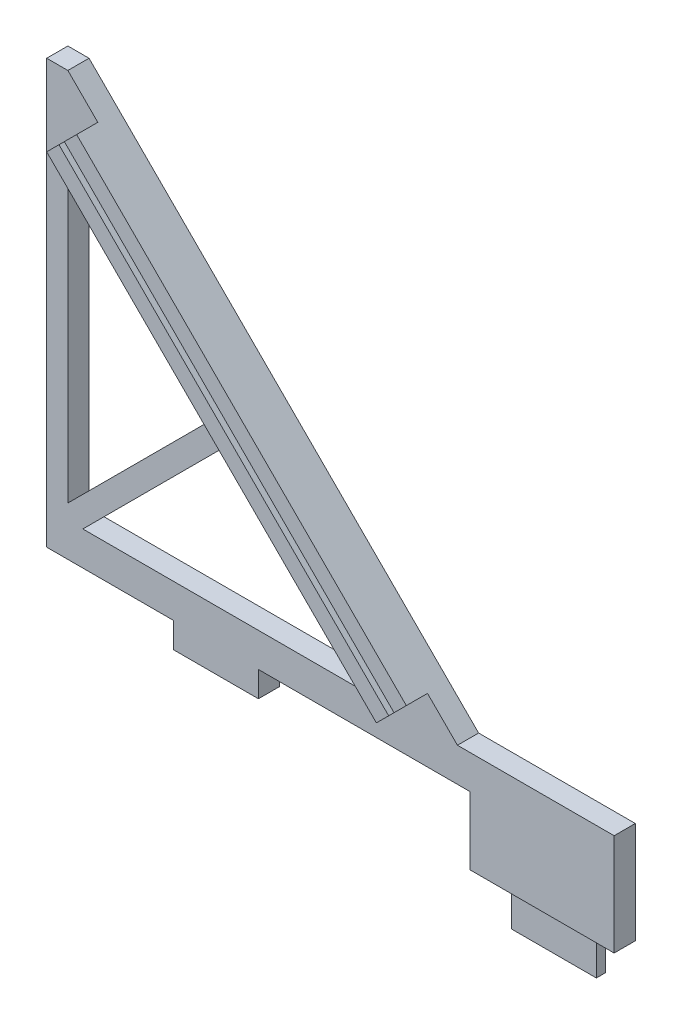
SolidWorks part; units mm, degrees
ref_plane "Front Plane" through (0, 0, 0) normal (0, 0, 1) x (1, 0, 0)
ref_plane "Top Plane" through (0, 0, 0) normal (0, 1, 0) x (1, 0, 0)
ref_plane "Right Plane" through (0, 0, 0) normal (1, 0, 0) x (0, 0, -1)
sketch "Sketch2" plane through (0, 0, 0) normal (0, 0, 1) x (1, 0, 0)
  line L0 (0, 0) -> (12.7, 0)
  line L1 (12.7, 0) -> (12.7, 6.35)
  line L2 (12.7, 6.35) -> (17.145, 6.35)
  line L3 (17.145, 6.35) -> (17.145, 21.59)
  line L5 (0, 0) -> (0, 6.35)
  line L6 (0, 6.35) -> (-4.445, 6.35)
  line L7 (-4.445, 6.35) -> (-4.445, 16.51)
  line L11 (-64.77, 80.01) -> (-67.945, 80.01)
  line L13 (-48.895, 16.51) -> (-48.895, 12.7)
  line L14 (-67.945, 80.01) -> (-67.945, 16.51)
  line L15 (-67.945, 16.51) -> (-48.895, 16.51)
  line L18 (-48.895, 12.7) -> (-36.195, 12.7)
  line L19 (-36.195, 12.7) -> (-36.195, 16.51)
  line L20 (-36.195, 16.51) -> (-4.445, 16.51)
  line L21 (17.145, 21.59) -> (-6.35, 21.59)
  line L22 (-6.35, 21.59) -> (-64.77, 80.01)
  line L23 (-64.77, 71.0297) -> (-64.77, 23.8351)
  line L24 (-62.5249, 21.59) -> (-15.3303, 21.59)
  line L25 (-15.3303, 21.59) -> (-38.9276, 45.1873)
  line L26 (-41.1727, 47.4324) -> (-64.77, 23.8351)
  line L27 (-38.9276, 45.1873) -> (-62.5249, 21.59)
  line L28 (-41.1727, 47.4324) -> (-64.77, 71.0297)
  point P16 (14.9225, 6.35)
  dimension "D1" = 63.5
  dimension "D2" = 12.7
  dimension "D3" = 4.445
  dimension "D4" = 4.445
  dimension "D5" = 6.35
  dimension "D6" = 6.35
  dimension "D7" = 45
  dimension "D8" = 6.35
  dimension "D9" = 5.08
  dimension "D10" = 3.175
  dimension "D11" = 6.35
  dimension "D12" = 15.24
  dimension "D13" = 6.35
  dimension "D14" = 31.75
  dimension "D15" = 12.7
  dimension "D16" = 3.81
  dimension "D17" = 3.175
extrude "Boss-Extrude1" add sketch "Sketch2" along normal blind 3.175
sketch "Sketch5" plane through (0, 0, 3.175) normal (0, 0, 1) x (1, 0, 0)
  line L1 (12.7, 0) -> (0, 0)
  line L2 (12.7, 0) -> (12.7, 6.35)
  line L3 (12.7, 6.35) -> (0, 6.35)
  line L4 (0, 0) -> (0, 6.35)
extrude "Cut-Extrude2" cut sketch "Sketch5" against normal blind 1.778
sketch "Sketch6" plane through (0, 0, 3.175) normal (0, 0, 1) x (1, 0, 0)
  line L0 (-15.3303, 21.59) -> (-64.77, 71.0297)
  line L1 (-64.77, 71.0297) -> (-62.929, 72.8707)
  line L2 (-62.929, 72.8707) -> (-13.4893, 23.431)
  line L3 (-13.4893, 23.431) -> (-15.3303, 21.59)
  line L4 (-10.8401, 26.0801) -> (-12.6811, 24.2392)
  line L5 (-6.35, 21.59) -> (-64.77, 80.01) construction
  line L6 (-12.6811, 24.2392) -> (-62.1208, 73.6789)
  line L7 (-62.1208, 73.6789) -> (-60.2799, 75.5199)
  line L8 (-60.2799, 75.5199) -> (-10.8401, 26.0801)
  dimension "D1" = 1.143
extrude "Boss-Extrude3" add sketch "Sketch6" along normal blind 3.175
sketch "Sketch7" plane through (0, 0, 3.175) normal (0, 0, 1) x (1, 0, 0)
  line L0 (-64.77, 76.119) -> (-10.241, 21.59) construction
  line L1 (-62.5249, 21.59) -> (-15.3303, 21.59) construction
  line L2 (-64.77, 71.0297) -> (-64.77, 23.8351) construction
  line L4 (-13.4893, 23.431) -> (-62.929, 72.8707) construction
